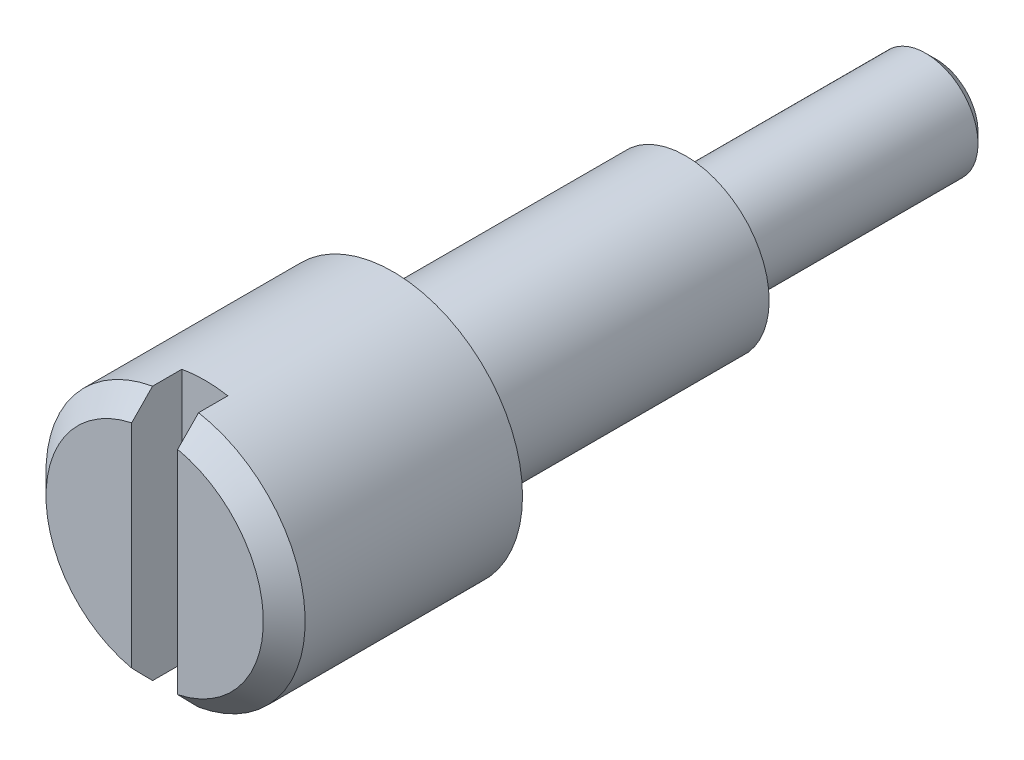
SolidWorks part; units mm, degrees
material "Латунь"
ref_plane "Спереди" through (0, 0, 0) normal (0, 0, 1) x (1, 0, 0)
ref_plane "Сверху" through (0, 0, 0) normal (0, 1, 0) x (1, 0, 0)
ref_plane "Справа" through (0, 0, 0) normal (1, 0, 0) x (0, 0, -1)
sketch "Эскиз1" plane through (0, 0, 0) normal (0, 0, 1) x (1, 0, 0)
  circle A0 centre (0, 0) radius 3.1
  dimension "D1" = 6.2
extrude "Бобышка-Вытянуть1" add sketch "Эскиз1" along normal blind 5.7
sketch "Эскиз2" plane through (0, 0, 0) normal (0, 0, -1) x (-1, 0, 0)
  circle A0 centre (0, 0) radius 2
  dimension "D1" = 4
extrude "Бобышка-Вытянуть2" add sketch "Эскиз2" along normal blind 7
sketch "Эскиз3" plane through (0, 0, -7) normal (0, 0, -1) x (-1, 0, 0)
  circle A0 centre (0, 0) radius 1.25
  dimension "D1" = 2.5
extrude "Бобышка-Вытянуть3" add sketch "Эскиз3" along normal blind 6
cosmetic thread "Условное изображение резьбы1" parameters "D1"=4.5, "D2"=1.993
chamfer "Фаска1" distance 0.2535 angle 45 1 edges at (-1.25, 0, -13)
chamfer "Фаска2" distance 0.5 angle 45 1 edges at (3.1, 0, 5.7)
sketch "Эскиз5" plane through (0, 0, 5.7) normal (0, 0, 1) x (1, 0, 0)
  line L1 (-0.55, -3.5) -> (0.55, -3.5)
  line L2 (-0.55, -3.5) -> (-0.55, 3.5)
  line L3 (-0.55, 3.5) -> (0.55, 3.5)
  line L4 (0.55, -3.5) -> (0.55, 3.5)
  line L5 (-0.55, -3.5) -> (0.55, 3.5) construction
  line L6 (-0.55, 3.5) -> (0.55, -3.5) construction
  point P0 (0, 0)
  dimension "D1" = 1.1
  dimension "D2" = 7
extrude "Вырез-Вытянуть1" cut sketch "Эскиз5" against normal blind 1.2
